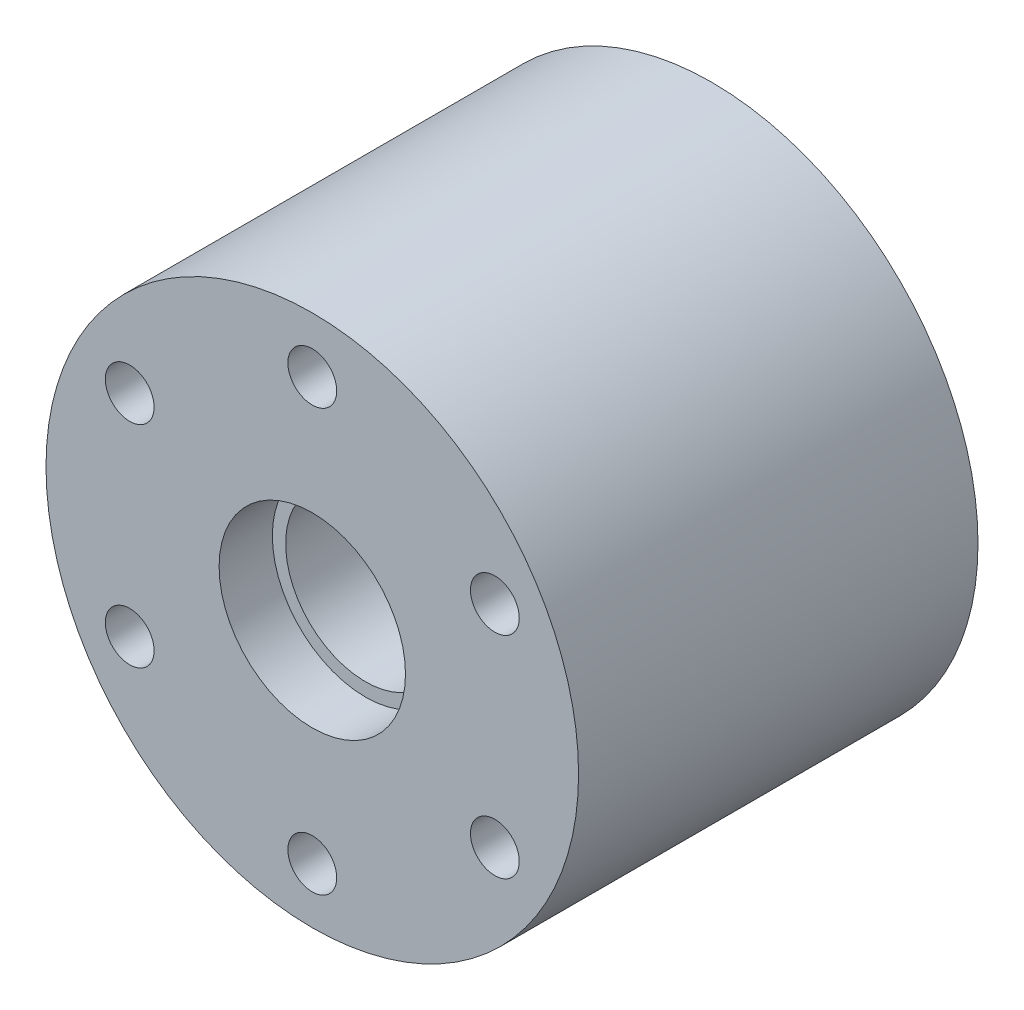
SolidWorks part; units mm, degrees
material "ABS"
ref_plane "Front Plane" through (0, 0, 0) normal (0, 0, 1) x (1, 0, 0)
ref_plane "Top Plane" through (0, 0, 0) normal (0, 1, 0) x (1, 0, 0)
ref_plane "Right Plane" through (0, 0, 0) normal (1, 0, 0) x (0, 0, -1)
sketch "Sketch1" plane through (0, 0, 0) normal (0, 0, 1) x (1, 0, 0)
  circle A0 centre (0, 0) radius 30
  circle A1 centre (0, 0) radius 9
  dimension "D1" = 60
  dimension "D2" = 18
extrude "Boss-Extrude1" add sketch "Sketch1" along normal blind 45
hole_wizard "M5 Clearance Hole1" positions "Sketch2" profile "Sketch3" hole size "M5" standard "DIN" end condition through all
sketch "Sketch2" plane through (0, 0, 45) normal (0, 0, 1) x (1, 0, 0)
  point P0 (0, 23.75)
  point P9 (20.5681, 11.875)
  point P10 (20.5681, -11.875)
  point P11 (0, -23.75)
  point P12 (-20.5681, -11.875)
  point P13 (-20.5681, 11.875)
  point P14 (0, 0)
  dimension "D1" = 23.75
  dimension "D2" = 6
sketch "Sketch3" plane through (0, 23.75, 45) normal (1, 0, 0) x (0, -1, 0)
  line L0 (0, 0) -> (0, 45)
  line L1 (0, 45) -> (2.75, 45)
  line L2 (2.75, 45) -> (2.75, 0)
  line L5 (2.75, 0) -> (0, 0)
  line L11 (0, -6.35) -> (0, 107.95) construction
  dimension "Thru Hole Dia." = 5.5
  dimension "Thru Hole Depth" = 45
sketch "Sketch4" plane through (0, 0, 45) normal (0, 0, 1) x (1, 0, 0)
  circle A0 centre (0, 0) radius 10.5
  dimension "D1" = 21
extrude "Cut-Extrude1" cut sketch "Sketch4" against normal blind 6
